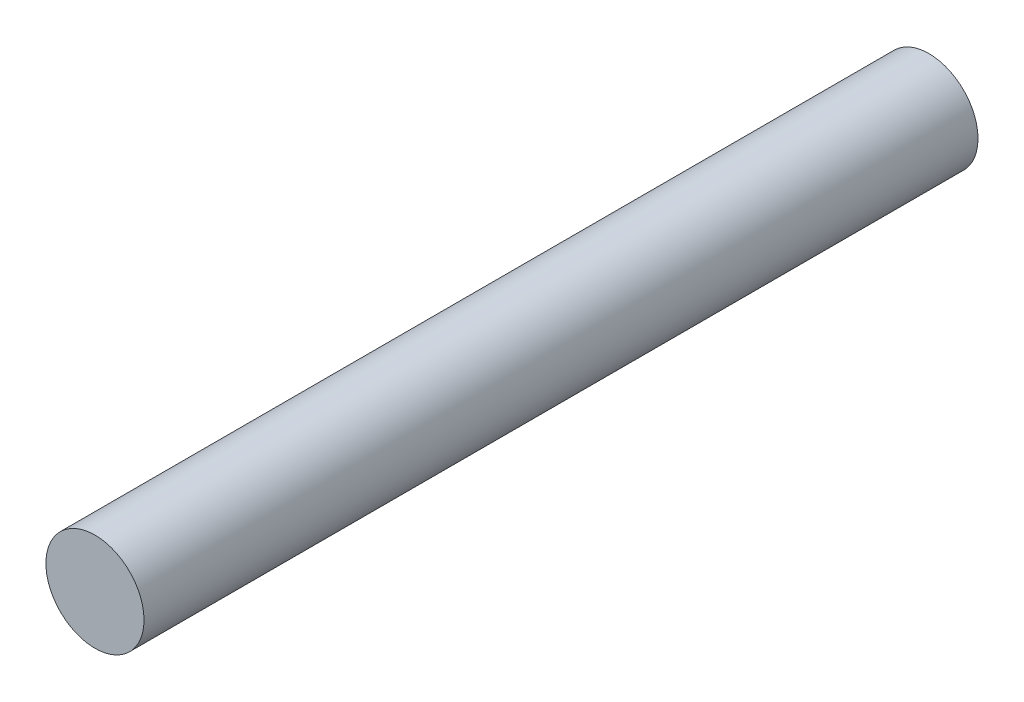
SolidWorks part; units mm, degrees
ref_plane "Plan de face" through (0, 0, 0) normal (0, 0, 1) x (1, 0, 0)
ref_plane "Plan de dessus" through (0, 0, 0) normal (0, 1, 0) x (1, 0, 0)
ref_plane "Plan de droite" through (0, 0, 0) normal (1, 0, 0) x (0, 0, -1)
sketch "Esquisse1" plane through (0, 0, 0) normal (0, 0, 1) x (1, 0, 0)
  circle A0 centre (0, 0) radius 2
  dimension "D1" = 4
extrude "Boss.-Extru.2" add sketch "Esquisse1" along normal blind 34 contours A0
